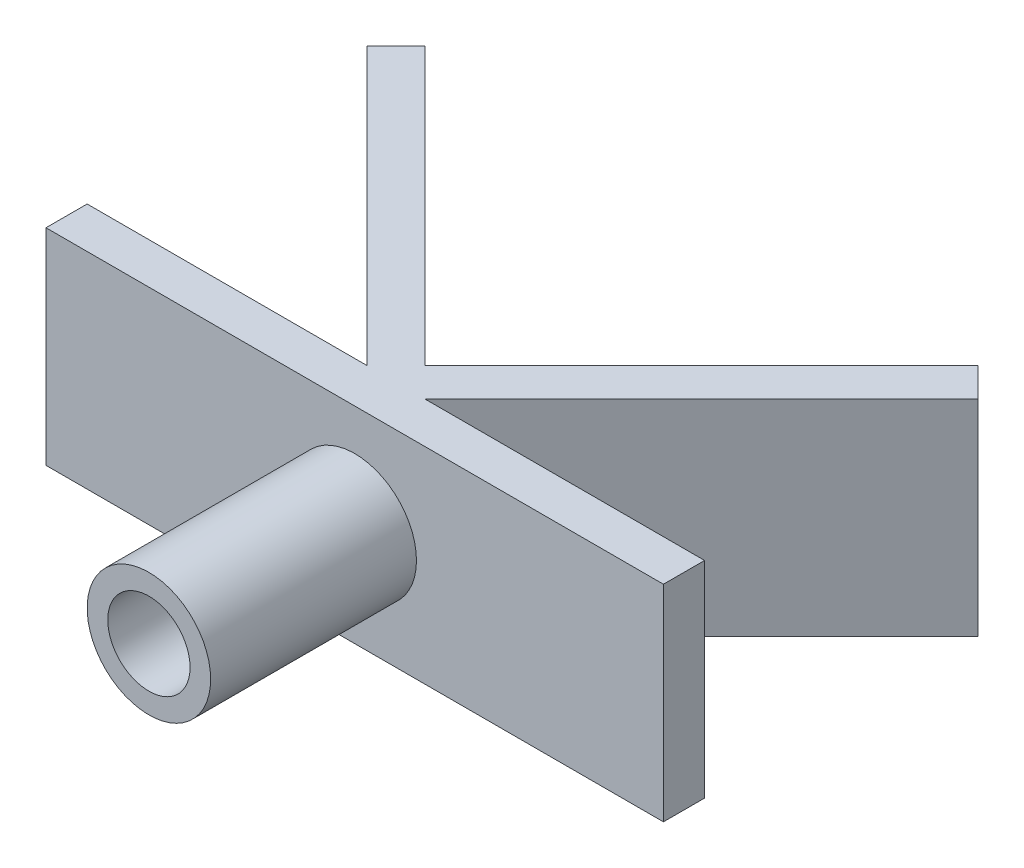
SolidWorks part; units mm, degrees
ref_plane "Alzado" through (0, 0, 0) normal (0, 0, 1) x (1, 0, 0)
ref_plane "Planta" through (0, 0, 0) normal (0, 1, 0) x (1, 0, 0)
ref_plane "Vista lateral" through (0, 0, 0) normal (1, 0, 0) x (0, 0, -1)
sketch "Sketch1" plane through (0, 0, 0) normal (0, 0, 1) x (1, 0, 0)
  circle A0 centre (0, 0) radius 2
  circle A1 centre (0, 0) radius 3
extrude "Boss-Extrude1" add sketch "Sketch1" along normal blind 10
ref_plane "Plane1" through (0, 0, 0) normal (0, 0, -1) x (-1, 0, 0)
sketch "Sketch2" plane through (0, 0, 0) normal (0, 0, -1) x (-1, 0, 0)
  line L2 (0, -5) -> (15, -5)
  line L3 (0, -5) -> (-15, -5)
  line L4 (-15, -5) -> (-15, 5)
  line L5 (-15, 5) -> (15, 5)
  line L6 (15, 5) -> (15, -5)
extrude "Boss-Extrude2" add sketch "Sketch2" along normal blind 2
sketch "Sketch3" plane through (0, 5, 0) normal (0, 1, 0) x (1, 0, 0)
  line L0 (0, 2) -> (-14.1421, 16.1421)
  line L1 (-15, 2) -> (15, 2) construction
  line L8 (-13.435, 16.8492) -> (0.7071, 2.7071)
  line L9 (-14.8492, 15.435) -> (-0.7071, 1.2929)
  line L10 (-0.7071, 1.2929) -> (0.7071, 2.7071)
  line L11 (0, 2) -> (14.1421, 16.1421)
  line L13 (-0.9352, 2.9352) -> (0.7071, 1.2929)
  line L16 (14.1421, 16.1421) -> (13.435, 16.8492)
  line L17 (14.1421, 16.1421) -> (14.8492, 15.435)
  line L18 (13.435, 16.8492) -> (0, 3.4142)
  line L19 (14.8492, 15.435) -> (0.7071, 1.2929)
  line L20 (0, 3.4142) -> (-0.7071, 2.7071)
  line L21 (0, 2) -> (-7.0711, 9.0711)
  line L22 (-14.1421, 16.1421) -> (-10.1987, 12.1987)
  line L24 (-14.1421, 16.1421) -> (-14.8492, 15.435)
  line L25 (-14.1421, 16.1421) -> (-13.435, 16.8492)
  point P7 (7.0711, 9.0711)
extrude "Boss-Extrude3" add sketch "Sketch3" against normal blind 10
